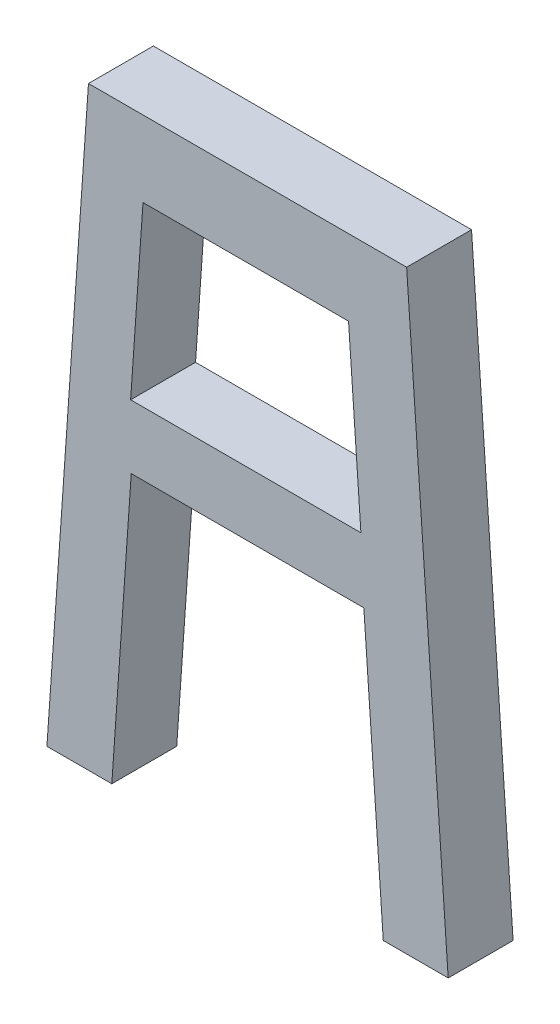
SolidWorks part; units mm, degrees
ref_plane "Front" through (0, 0, 0) normal (0, 0, 1) x (1, 0, 0)
ref_plane "Top" through (0, 0, 0) normal (0, 1, 0) x (1, 0, 0)
ref_plane "Right" through (0, 0, 0) normal (1, 0, 0) x (0, 0, -1)
sketch "Sketch1" plane through (0, 0, 0) normal (0, 0, 1) x (1, 0, 0)
  line L0 (-39.259, 44.2967) -> (-31.1281, 160.684)
  line L1 (-31.1281, 160.684) -> (31.1281, 160.684)
  line L2 (31.1281, 160.684) -> (39.259, 44.2967)
  line L3 (-39.259, 44.2967) -> (-26.559, 44.2967)
  line L4 (39.259, 44.2967) -> (26.559, 44.2967)
  line L5 (-26.559, 44.2967) -> (-22.7539, 98.7634)
  line L6 (-22.7539, 98.7634) -> (22.7539, 98.7634)
  line L7 (22.7539, 98.7634) -> (26.559, 44.2967)
  point P7 (0, 160.684)
  point P9 (0, 98.7634)
  dimension "D1" = 116.3873
  dimension "D2" = 12.7
  dimension "D3" = 12.7
  dimension "D4" = 54.4667
extrude "Boss-Extrude1" add sketch "Sketch1" along normal blind 12.7 contours L6 L7 L4 L2 L1 L0 L3 L5
sketch "Sketch5" plane through (0, 0, 12.7) normal (0, 0, 1) x (1, 0, 0)
  line L0 (-20.4587, 145.8486) -> (-22.8789, 111.2045)
  line L1 (-39.259, 44.2967) -> (-31.1281, 160.684) construction
  line L2 (-22.8789, 111.2045) -> (22.1824, 111.2045)
  line L3 (22.1824, 111.2045) -> (19.7621, 145.8486)
  line L4 (19.7621, 145.8486) -> (-20.4587, 145.8486)
  line L5 (31.1281, 160.684) -> (39.259, 44.2967) construction
  line L6 (-31.1281, 160.684) -> (31.1281, 160.684) construction
  line L7 (-22.7539, 98.7634) -> (22.7539, 98.7634) construction
  dimension "D1" = 45.0613
  dimension "D2" = 34.644
  dimension "D3" = 34.644
  dimension "D4" = 40.2208
extrude "Cut-Extrude3" cut sketch "Sketch5" against normal blind 12.7
